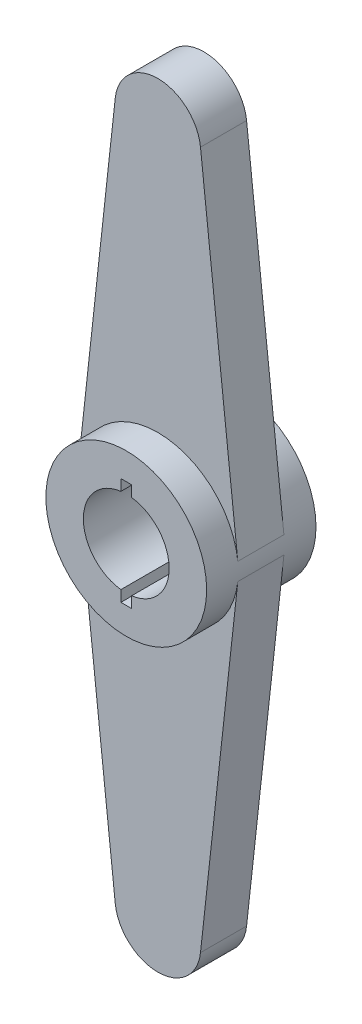
SolidWorks part; units mm, degrees
ref_plane "Ebene vorne" through (0, 0, 0) normal (0, 0, 1) x (1, 0, 0)
ref_plane "Ebene oben" through (0, 0, 0) normal (0, 1, 0) x (1, 0, 0)
ref_plane "Ebene rechts" through (0, 0, 0) normal (1, 0, 0) x (0, 0, -1)
sketch "Sketch1" plane through (0, 0, 0) normal (0, 0, 1) x (1, 0, 0)
  line L0 (-3.7276, 0.4089) -> (-1.9881, 16.2681)
  line L1 (0, 21.498) -> (0, -6.4772) construction
  line L2 (3.7276, 0.4089) -> (1.9881, 16.2681)
  line L3 (0, 0) -> (-15.4081, 0) construction
  line L4 (3.7276, -0.4089) -> (1.9881, -16.2681)
  line L5 (-3.7276, -0.4089) -> (-1.9881, -16.2681)
  line L7 (0.25, -2.5) -> (-0.25, -2.5)
  line L8 (0.25, -2.5) -> (0.25, 2.5)
  line L9 (0.25, 2.5) -> (-0.25, 2.5)
  line L10 (-0.25, -2.5) -> (-0.25, 2.5)
  line L11 (0.25, -2.5) -> (-0.25, 2.5) construction
  line L12 (0.25, 2.5) -> (-0.25, -2.5) construction
  circle A0 centre (0, 0) radius 3.75
  arc A2 (1.9881, -16.2681) -> (-1.9881, -16.2681) centre (0, -16.05) cw
  arc A3 (1.9881, 16.2681) -> (-1.9881, 16.2681) centre (0, 16.05) ccw
  circle A4 centre (0, 0) radius 2
  point P17 (0, 0)
  dimension "D1" = 7.5
  dimension "D2" = 0.5
  dimension "D4" = 4
  dimension "D3" = 5
extrude "Boss-Extrude1" add sketch "Sketch1" along normal mid plane 5.1 contours A0 A4 L10 L9 L8 L7
sketch "Sketch2" plane through (0, 0, 0) normal (0, 0, 1) x (1, 0, 0)
  line L0 (-3.7276, -0.4089) -> (-1.9881, -16.2681) construction
  line L1 (3.7276, -0.4089) -> (1.9881, -16.2681) construction
  line L2 (3.7276, 0.4089) -> (1.9881, 16.2681) construction
  line L3 (-3.7276, 0.4089) -> (-1.9881, 16.2681) construction
  line L4 (-3.7276, -0.4089) -> (-1.9881, -16.2681)
  line L5 (3.7276, -0.4089) -> (1.9881, -16.2681)
  line L6 (3.7276, 0.4089) -> (1.9881, 16.2681)
  line L7 (-3.7276, 0.4089) -> (-1.9881, 16.2681)
  arc A0 (-1.9881, -16.2681) -> (1.9881, -16.2681) centre (0, -16.05) ccw construction
  circle A1 centre (0, 0) radius 3.75 construction
  arc A2 (1.9881, 16.2681) -> (-1.9881, 16.2681) centre (0, 16.05) ccw construction
  arc A3 (-1.9881, -16.2681) -> (1.9881, -16.2681) centre (0, -16.05) ccw
  circle A4 centre (0, 0) radius 3.75
  arc A5 (1.9881, 16.2681) -> (-1.9881, 16.2681) centre (0, 16.05) ccw
extrude "Boss-Extrude2" add sketch "Sketch2" along normal mid plane 2.15 contours L6 A5 L7 A4 | A4 L4 A3 L5
